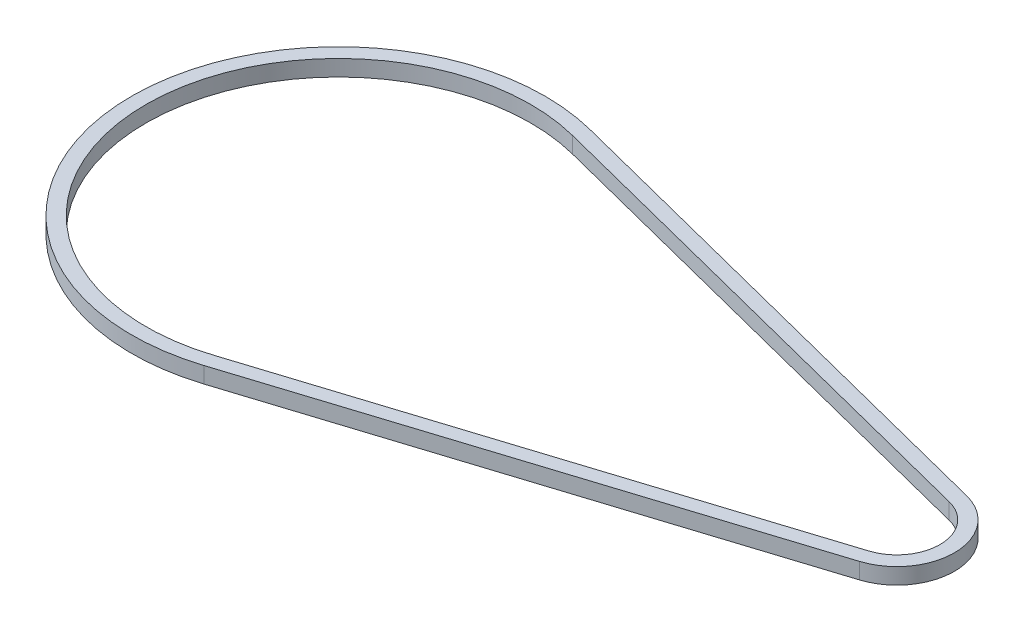
SolidWorks part; units mm, degrees
ref_plane "Front Plane" through (0, 0, 0) normal (0, 0, 1) x (1, 0, 0)
ref_plane "Top Plane" through (0, 0, 0) normal (0, 1, 0) x (1, 0, 0)
ref_plane "Right Plane" through (0, 0, 0) normal (1, 0, 0) x (0, 0, -1)
sketch "Sketch1" plane through (0, 0, 0) normal (0, 1, 0) x (1, 0, 0)
  line L0 (-166.0826, 101.4122) -> (98.0832, 34.0834)
  line L1 (-192.7561, -3.2421) -> (90.6739, 5.0128) construction
  line L2 (-160.0368, -106.1665) -> (99.7626, -23.5773)
  line L3 (-162.309, -99.019) -> (97.4904, -16.4298)
  line L4 (-167.9349, 94.1446) -> (96.2309, 26.8158)
  arc A0 (-166.0826, 101.4122) -> (-160.0368, -106.1665) centre (-192.7561, -3.2421) ccw
  arc A1 (99.7626, -23.5773) -> (98.0832, 34.0834) centre (90.6739, 5.0128) ccw
  arc A2 (-167.9349, 94.1446) -> (-162.309, -99.019) centre (-192.7561, -3.2421) ccw
  arc A3 (97.4904, -16.4298) -> (96.2309, 26.8158) centre (90.6739, 5.0128) ccw
  dimension "D1" = 216
  dimension "D2" = 60
  dimension "D4" = 283.43
  dimension "D3" = 7.5
extrude "Boss-Extrude1" add sketch "Sketch1" along normal blind 8.4
